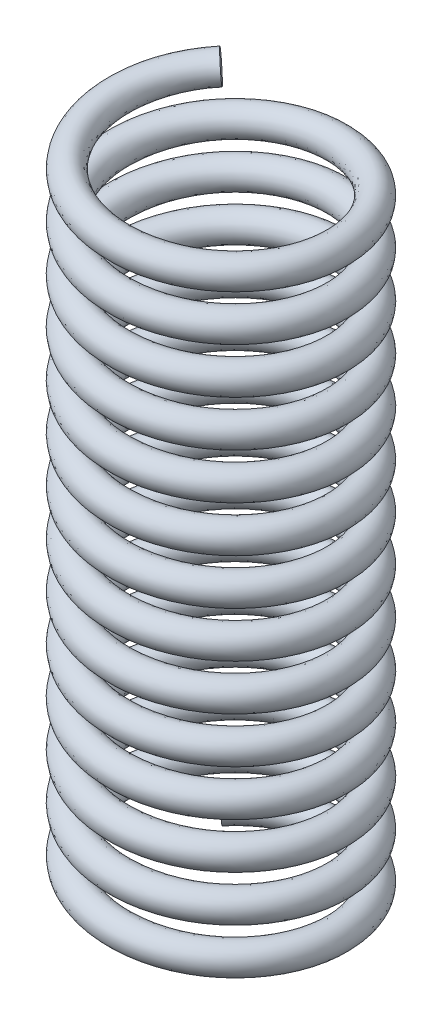
SolidWorks part; units mm, degrees
ref_plane "Front Plane" through (0, 0, 0) normal (0, 0, 1) x (1, 0, 0)
ref_plane "Top Plane" through (0, 0, 0) normal (0, 1, 0) x (1, 0, 0)
ref_plane "Right Plane" through (0, 0, 0) normal (1, 0, 0) x (0, 0, -1)
sketch "Sketch1" plane through (0, 0, 0) normal (0, 1, 0) x (1, 0, 0)
  circle A0 centre (0, 0) radius 3.75
  dimension "D1" = 7.5
curve "Helix/Spiral1" pitch 1.5714 height 22 turns 14
sweep "Sweep1" add path "Helix/Spiral1" circular profile diameter 1 parameters "D3"=1
